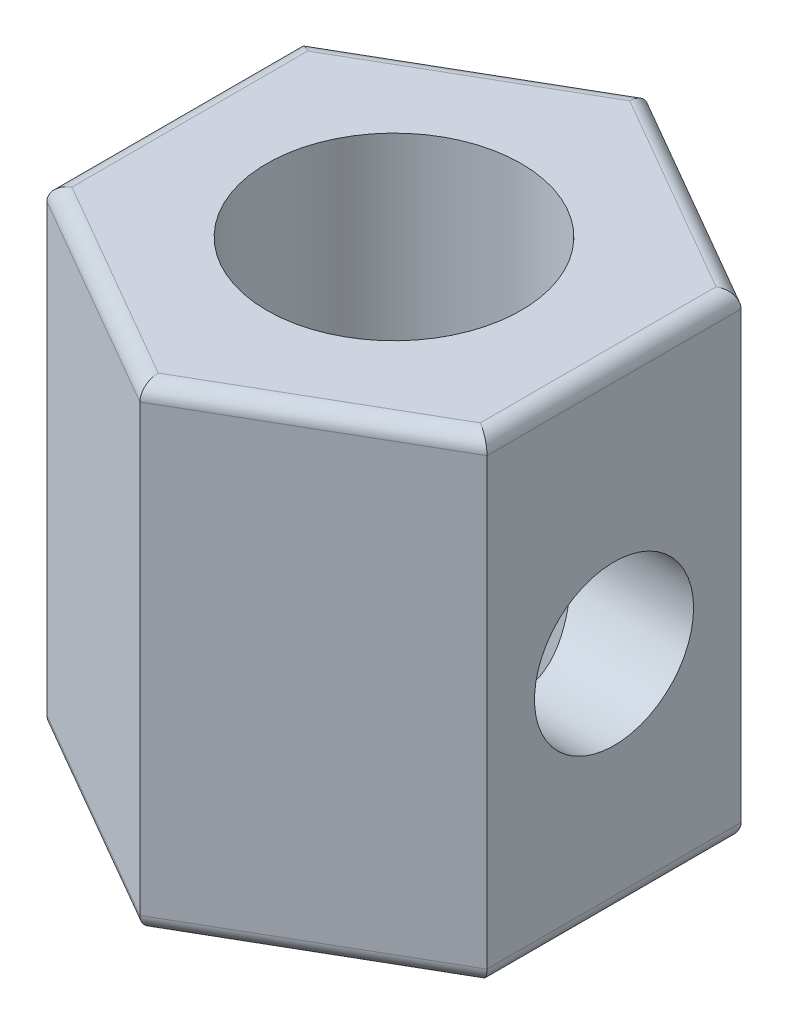
SolidWorks part; units mm, degrees
material "1023 Carbon Steel Sheet (SS)"
ref_plane "Front Plane" through (0, 0, 0) normal (0, 0, 1) x (1, 0, 0)
ref_plane "Top Plane" through (0, 0, 0) normal (0, 1, 0) x (1, 0, 0)
ref_plane "Right Plane" through (0, 0, 0) normal (1, 0, 0) x (0, 0, -1)
sketch "Sketch1" plane through (0, 0, 0) normal (0, 1, 0) x (1, 0, 0)
  line L0 (0, 4) -> (0, -4) construction
  line L2 (0, 4) -> (-3.4641, 2)
  line L3 (-3.4641, 2) -> (-3.4641, -2)
  line L4 (-3.4641, -2) -> (0, -4)
  line L5 (0, -4) -> (3.4641, -2)
  line L6 (3.4641, -2) -> (3.4641, 2)
  line L7 (3.4641, 2) -> (0, 4)
  circle A0 centre (0, 0) radius 4 construction
  circle A1 centre (0, 0) radius 2.0025
  dimension "D2" = 4.005
  dimension "D1" = 8
extrude "Boss-Extrude1" add sketch "Sketch1" along normal blind 7.5
hole_wizard "M3x0.5 Tapped Hole1" positions "3DSketch1" profile "Sketch2" tap size "M3x0.5" standard "JIS"
sketch3d "3DSketch1"
  line L0 (3.4641, 7.5, -2) -> (3.4641, 0, -2) construction
  line L1 (3.4641, 0, 2) -> (3.4641, 0, -2) construction
  point P0 (3.4641, 3.55, 0)
  dimension "D1" = 2
  dimension "D2" = 3.55
sketch "Sketch2" plane through (3.4641, 3.55, 0) normal (0, 1, 0) x (0, 0, -1)
  line L0 (0, 0) -> (0, 1.4616)
  line L1 (0, 1.4616) -> (1.2525, 1.4616)
  line L2 (1.2525, 1.4616) -> (1.2525, 0)
  line L5 (1.2525, 0) -> (0, 0)
  line L11 (0, -6.35) -> (0, 107.95) construction
  dimension "Thru Tap Drill Dia." = 2.505
  dimension "Thru Tap Drill Depth" = 1.4616
cosmetic thread "Hole Thread1" parameters "D2"=3
fillet "Fillet1" radius 0.25 12 edges at (1.7321, 0, 3) (3.4641, 0, 0) (1.7321, 0, -3) (-1.7321, 0, -3) (-3.4641, 0, 0) (-1.7321, 0, 3) (1.7321, 7.5, -3) (-1.7321, 7.5, -3) (-3.4641, 7.5, 0) (-1.7321, 7.5, 3) (1.7321, 7.5, 3) (3.4641, 7.5, 0)
